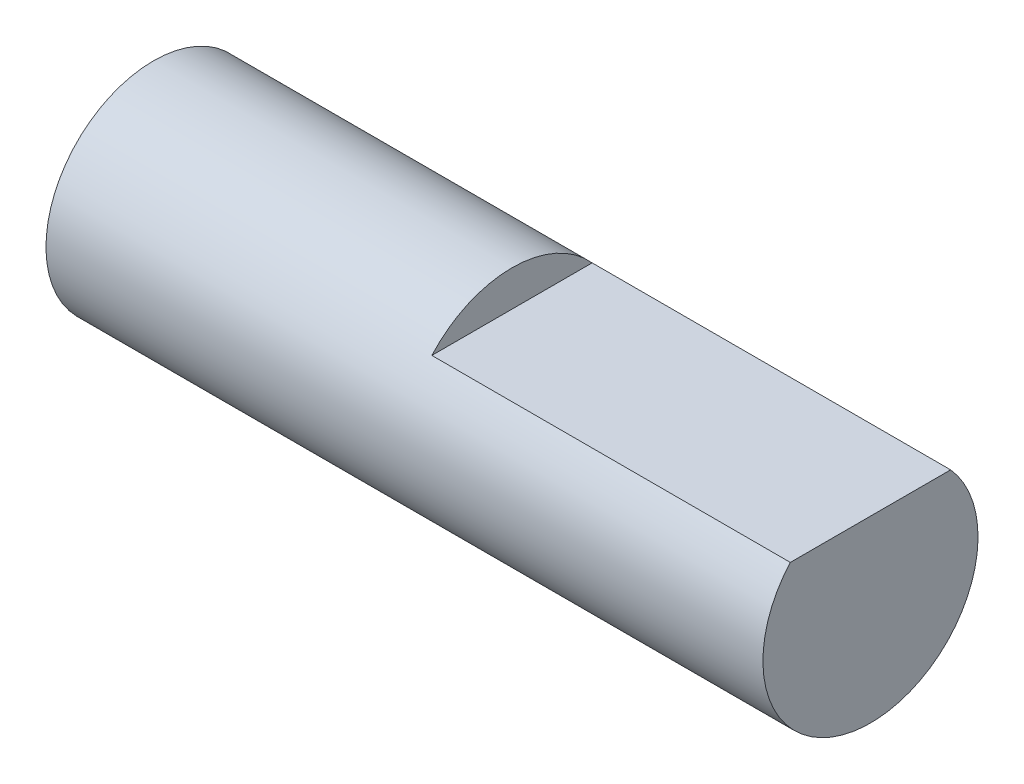
SolidWorks part; units mm, degrees
ref_plane "Ön Düzlem" through (0, 0, 0) normal (0, 0, 1) x (1, 0, 0)
ref_plane "Üst Düzlem" through (0, 0, 0) normal (0, 1, 0) x (1, 0, 0)
ref_plane "Sağ Düzlem" through (0, 0, 0) normal (1, 0, 0) x (0, 0, -1)
sketch "Sketch2" plane through (0, 0, 0) normal (1, 0, 0) x (0, 0, -1)
  circle A0 centre (0, 0) radius 3
extrude "Boss-Extrude2" add sketch "Sketch2" along normal blind 20
sketch "Sketch3" plane through (20, 0, 0) normal (1, 0, 0) x (0, 0, -1)
  line L0 (-2.2361, 2) -> (2.2361, 2)
  circle A0 centre (0, 0) radius 3 construction
  arc A1 (2.2361, 2) -> (-2.2361, 2) centre (0, 0) ccw
  dimension "D1" = 2
extrude "Cut-Extrude1" cut sketch "Sketch3" against normal blind 10
